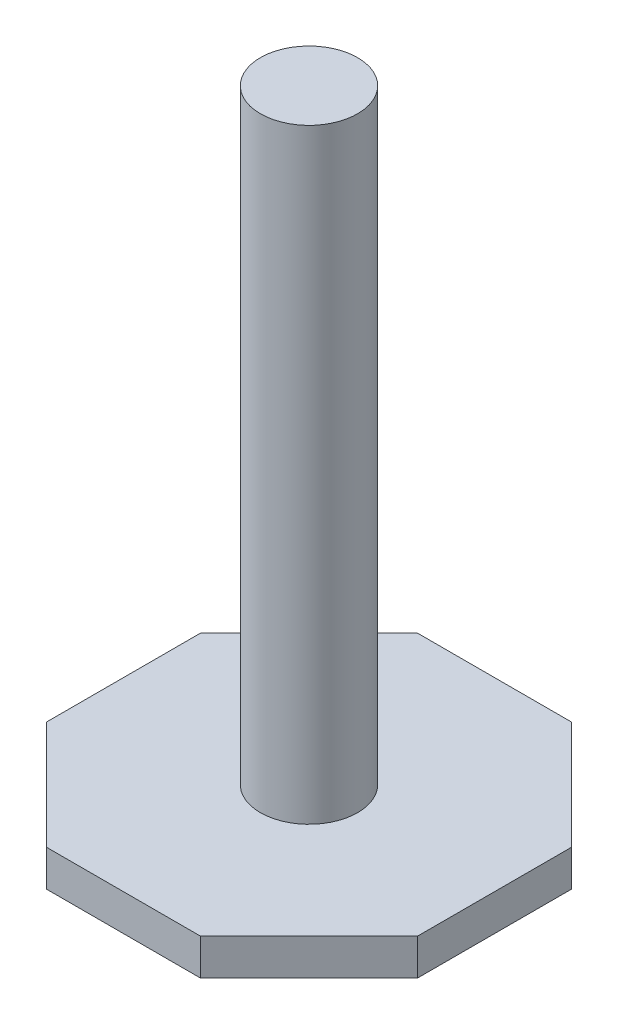
SolidWorks part; units mm, degrees
ref_plane "정면" through (0, 0, 0) normal (0, 0, 1) x (1, 0, 0)
ref_plane "윗면" through (0, 0, 0) normal (0, 1, 0) x (1, 0, 0)
ref_plane "우측면" through (0, 0, 0) normal (1, 0, 0) x (0, 0, -1)
sketch "스케치1" plane through (0, 0, 0) normal (0, 1, 0) x (1, 0, 0)
  circle A0 centre (0, 0) radius 4.015
  dimension "D1" = 8.03
extrude "보스-돌출1" add sketch "스케치1" along normal blind 50
sketch "스케치2" plane through (0, 0, 0) normal (0, -1, 0) x (1, 0, 0)
  line L0 (55, 0) -> (-55, 0) construction
  line L1 (5.9316, -14.3201) -> (14.3201, -5.9316)
  line L2 (14.3201, -5.9316) -> (14.3201, 5.9316)
  line L3 (14.3201, 5.9316) -> (5.9316, 14.3201)
  line L4 (5.9316, 14.3201) -> (-5.9316, 14.3201)
  line L5 (-5.9316, 14.3201) -> (-14.3201, 5.9316)
  line L6 (-14.3201, 5.9316) -> (-14.3201, -5.9316)
  line L7 (-14.3201, -5.9316) -> (-5.9316, -14.3201)
  line L8 (-5.9316, -14.3201) -> (5.9316, -14.3201)
  line L9 (6.3458, -15.3201) -> (15.3201, -6.3458)
  line L10 (15.3201, -6.3458) -> (15.3201, 6.3458)
  line L11 (15.3201, 6.3458) -> (6.3458, 15.3201)
  line L12 (6.3458, 15.3201) -> (-6.3458, 15.3201)
  line L13 (-6.3458, 15.3201) -> (-15.3201, 6.3458)
  line L14 (-15.3201, 6.3458) -> (-15.3201, -6.3458)
  line L15 (-15.3201, -6.3458) -> (-6.3458, -15.3201)
  line L16 (-6.3458, -15.3201) -> (6.3458, -15.3201)
  line L17 (5.5174, -13.3201) -> (13.3201, -5.5174)
  line L18 (13.3201, -5.5174) -> (13.3201, 5.5174)
  line L19 (13.3201, 5.5174) -> (5.5174, 13.3201)
  line L20 (5.5174, 13.3201) -> (-5.5174, 13.3201)
  line L21 (-5.5174, 13.3201) -> (-13.3201, 5.5174)
  line L22 (-13.3201, 5.5174) -> (-13.3201, -5.5174)
  line L23 (-13.3201, -5.5174) -> (-5.5174, -13.3201)
  line L24 (-5.5174, -13.3201) -> (5.5174, -13.3201)
  circle A0 centre (0, 0) radius 15.5 construction
  dimension "D1" = 31
  dimension "D2" = 1
  dimension "D3" = 1
extrude "보스-돌출2" add sketch "스케치2" along normal blind 3 contours L12 L13 L14 L15 L16 L9 L10 L11
sketch "스케치3" plane through (0, -3, 0) normal (0, -1, 0) x (1, 0, 0)
  line L0 (55, 0) -> (-55, 0) construction
  line L1 (5.9316, -14.3201) -> (14.3201, -5.9316)
  line L2 (14.3201, -5.9316) -> (14.3201, 5.9316)
  line L3 (14.3201, 5.9316) -> (5.9316, 14.3201)
  line L4 (5.9316, 14.3201) -> (-5.9316, 14.3201)
  line L5 (-5.9316, 14.3201) -> (-14.3201, 5.9316)
  line L6 (-14.3201, 5.9316) -> (-14.3201, -5.9316)
  line L7 (-14.3201, -5.9316) -> (-5.9316, -14.3201)
  line L8 (-5.9316, -14.3201) -> (5.9316, -14.3201)
  line L9 (6.3458, -15.3201) -> (15.3201, -6.3458)
  line L10 (15.3201, -6.3458) -> (15.3201, 6.3458)
  line L11 (15.3201, 6.3458) -> (6.3458, 15.3201)
  line L12 (6.3458, 15.3201) -> (-6.3458, 15.3201)
  line L13 (-6.3458, 15.3201) -> (-15.3201, 6.3458)
  line L14 (-15.3201, 6.3458) -> (-15.3201, -6.3458)
  line L15 (-15.3201, -6.3458) -> (-6.3458, -15.3201)
  line L16 (-6.3458, -15.3201) -> (6.3458, -15.3201)
  line L17 (5.5174, -13.3201) -> (13.3201, -5.5174)
  line L18 (13.3201, -5.5174) -> (13.3201, 5.5174)
  line L19 (13.3201, 5.5174) -> (5.5174, 13.3201)
  line L20 (5.5174, 13.3201) -> (-5.5174, 13.3201)
  line L21 (-5.5174, 13.3201) -> (-13.3201, 5.5174)
  line L22 (-13.3201, 5.5174) -> (-13.3201, -5.5174)
  line L23 (-13.3201, -5.5174) -> (-5.5174, -13.3201)
  line L24 (-5.5174, -13.3201) -> (5.5174, -13.3201)
  circle A0 centre (0, 0) radius 15.5 construction
  dimension "D1" = 31
  dimension "D2" = 1
  dimension "D3" = 1
extrude "컷-돌출1" cut sketch "스케치3" against normal blind 1 contours L7 L8 L1 L2 L3 L4 L5 L6 L24 L23 L22 L21 L20 L19 L18 L17
